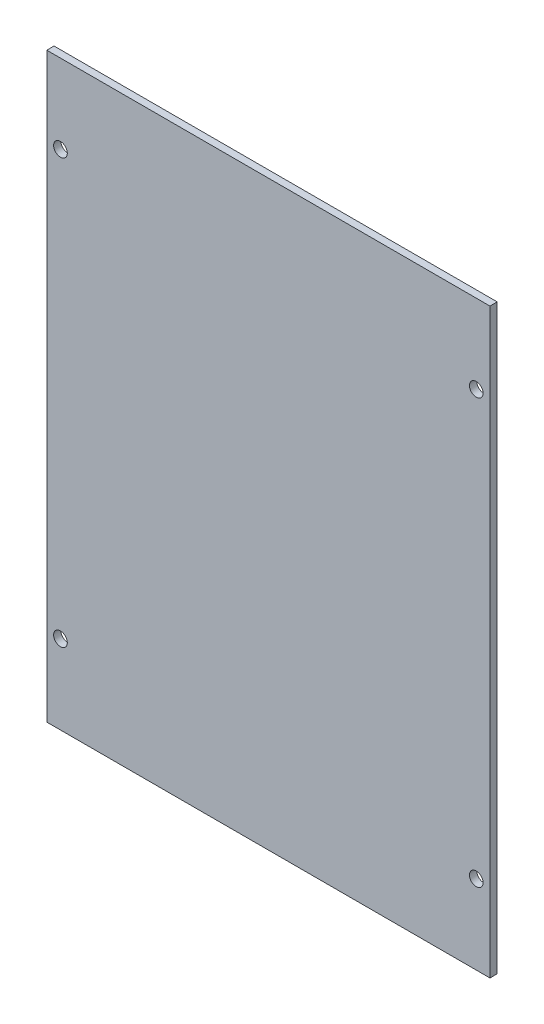
SolidWorks part; units mm, degrees
material "6061-T6 Al"
ref_plane "Front Plane" through (0, 0, 0) normal (0, 0, 1) x (1, 0, 0)
ref_plane "Top Plane" through (0, 0, 0) normal (0, 1, 0) x (1, 0, 0)
ref_plane "Right Plane" through (0, 0, 0) normal (1, 0, 0) x (0, 0, -1)
sketch "Sketch1" plane through (0, 0, 0) normal (0, 0, 1) x (1, 0, 0)
  line L1 (-73.025, 95.885) -> (73.025, 95.885)
  line L2 (-73.025, 95.885) -> (-73.025, -95.885)
  line L3 (-73.025, -95.885) -> (73.025, -95.885)
  line L4 (73.025, 95.885) -> (73.025, -95.885)
  point P4 (-73.025, 0)
  point P6 (0, 95.885)
  dimension "D1" = 191.77
  dimension "D2" = 146.05
extrude "Boss-Extrude1" add sketch "Sketch1" along normal mid plane 2.3876
hole_wizard "#8 Clearance Hole1" positions "3DSketch1" profile "Sketch8" hole size "#8" standard "ANSI Inch" end condition through all
sketch3d "3DSketch1"
  line L0 (-68.5165, 69.85, 1.1938) -> (0, 0, 1.1938) construction
  line L1 (0, 0, 1.1938) -> (68.5165, -69.85, 1.1938) construction
  point P0 (68.5165, 69.85, 1.1938)
  point P3 (-68.5165, 69.85, 1.1938)
  point P6 (-68.5165, -69.85, 1.1938)
  point P9 (68.5165, -69.85, 1.1938)
  dimension "D1" = 137.033
  dimension "D2" = 139.7
sketch "Sketch8" plane through (68.5165, 69.85, 1.1938) normal (1, 0, 0) x (0, -1, 0)
  line L0 (0, 0) -> (0, 2.3876)
  line L1 (0, 2.3876) -> (2.2479, 2.3876)
  line L2 (2.2479, 2.3876) -> (2.2479, 0)
  line L5 (2.2479, 0) -> (0, 0)
  line L11 (0, -6.35) -> (0, 107.95) construction
  dimension "Thru Hole Dia." = 4.4958
  dimension "Thru Hole Depth" = 2.3876
